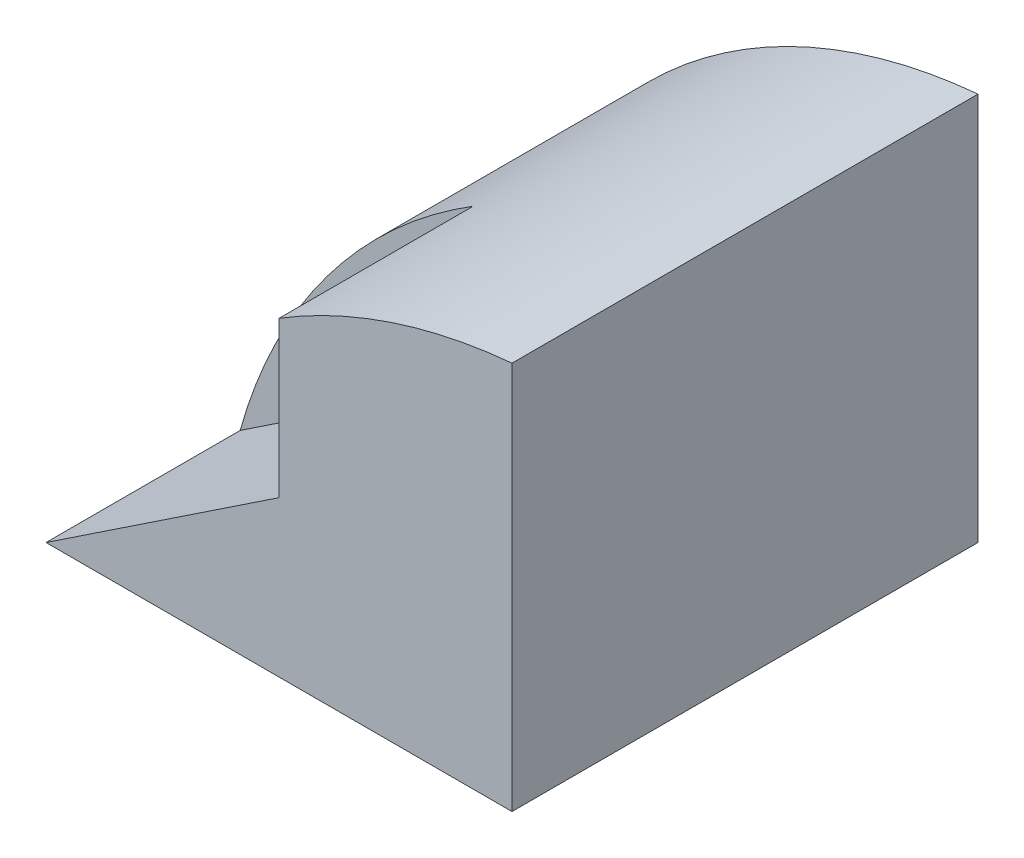
SolidWorks part; units mm, degrees
ref_plane "Front" through (0, 0, 0) normal (0, 0, 1) x (1, 0, 0)
ref_plane "Top" through (0, 0, 0) normal (0, 1, 0) x (1, 0, 0)
ref_plane "Right" through (0, 0, 0) normal (1, 0, 0) x (0, 0, -1)
sketch "Sketch1" plane through (0, 0, 0) normal (0, 1, 0) x (1, 0, 0)
  line L1 (-3, -3) -> (3, -3)
  line L2 (-3, -3) -> (-3, 3)
  line L3 (-3, 3) -> (3, 3)
  line L4 (3, -3) -> (3, 3)
  line L5 (-3, -3) -> (3, 3) construction
  line L6 (-3, 3) -> (3, -3) construction
  point P0 (0, 0)
  dimension "D1" = 6
  dimension "D2" = 6
extrude "Boss-Extrude1" add sketch "Sketch1" along normal blind 5
sketch "Sketch11" plane through (0, 0, 3) normal (0, 0, 1) x (1, 0, 0)
  line L0 (3, 5) -> (3, 0) construction
  line L1 (-3, 0) -> (3, 0) construction
  line L6 (-3, 0) -> (3, 0)
  line L7 (3, 0) -> (3, 5)
  line L8 (3, 5) -> (-3, 5)
  line L9 (-3, 5) -> (-3, 0)
  line L10 (-3, 0) -> (3, 0)
  line L11 (3, 0) -> (3, 5)
  line L12 (3, 5) -> (-3, 5)
  line L13 (-3, 5) -> (-3, 0)
  arc A0 (-3, 0) -> (3, 5) centre (3.6111, -1.8333) cw
  point P3 (0, 4)
  line M7 (3, 5) -> (-3, 5)
  line M8 (-3, 5) -> (-3, 0)
  dimension "D1" = 3
  dimension "D2" = 4
  dimension "D3" = 0
extrude "Cut-Extrude10" cut sketch "Sketch11" against normal blind 12.5 contours A0 M8 M7
sketch "Sketch12" plane through (0, 0, 3) normal (0, 0, 1) x (1, 0, 0)
  line L0 (0, 4) -> (0, 2)
  line L1 (0, 2) -> (-3, 0)
  line L2 (3, 0) -> (3, 5)
  line L3 (-3, 0) -> (3, 0)
  line L4 (3, 0) -> (3, 5)
  line L5 (-3, 0) -> (3, 0)
  arc A1 (3, 5) -> (-3, 0) centre (3.6111, -1.8333) ccw
  arc A2 (3, 5) -> (-3, 0) centre (3.6111, -1.8333) ccw
  arc M6 (3, 5) -> (-3, 0) centre (3.6111, -1.8333) ccw
  dimension "D2" = 2
  dimension "D1" = 0
extrude "Cut-Extrude11" cut sketch "Sketch12" against normal blind 2.5 contours L1 L0 M6
